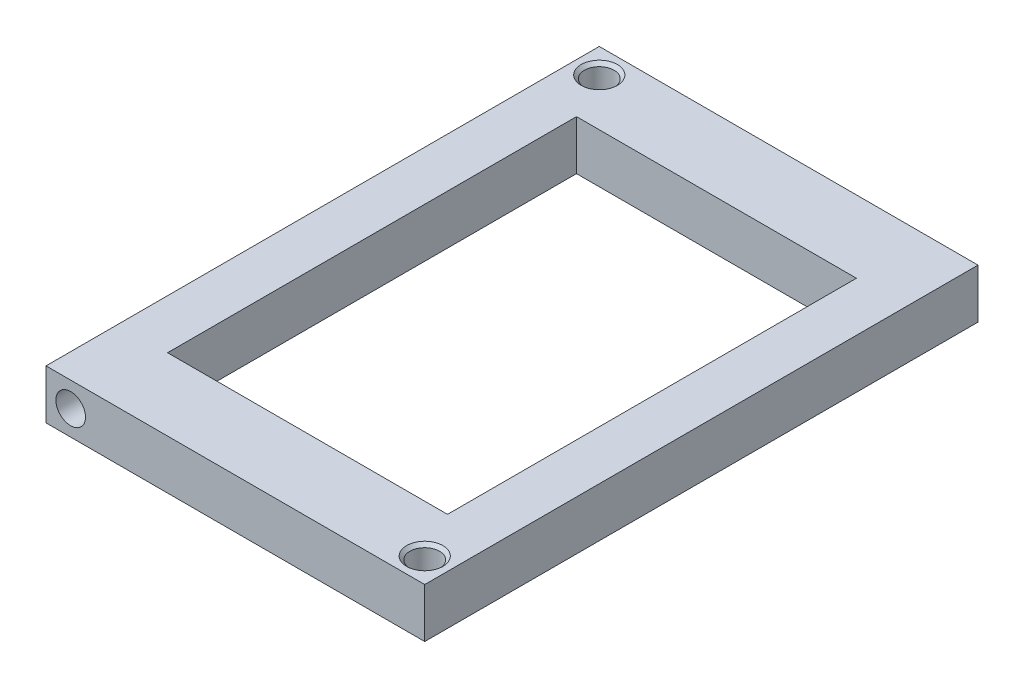
SolidWorks part; units mm, degrees
ref_plane "Plan de face" through (0, 0, 0) normal (0, 0, 1) x (1, 0, 0)
ref_plane "Plan de dessus" through (0, 0, 0) normal (0, 1, 0) x (1, 0, 0)
ref_plane "Plan de droite" through (0, 0, 0) normal (1, 0, 0) x (0, 0, -1)
sketch "Esquisse1" plane through (0, 0, 0) normal (0, 0, 1) x (1, 0, 0)
  line L0 (-15.8423, 13.6674) -> (-23.3423, 13.6674)
  line L1 (-15.8423, 13.6674) -> (26.6577, 13.6674)
  line L5 (-23.3423, 21.1674) -> (34.1577, 21.1674)
  line L6 (-23.3423, 21.1674) -> (-23.3423, 13.6674)
  line L8 (34.1577, 21.1674) -> (34.1577, 13.6674)
  line L9 (26.6577, 13.6674) -> (34.1577, 13.6674)
  line L10 (-23.3423, 21.1674) -> (-15.8423, 13.6674) construction
  dimension "D1" = 42.5
  dimension "D2" = 45
  dimension "D3" = 57.5
  dimension "D5" = 7.5
extrude "Boss.-Extru.1" add sketch "Esquisse1" along normal blind 84
sketch "Esquisse3" plane through (0, 0, 84) normal (0, 0, 1) x (1, 0, 0)
  line L0 (-23.3423, 21.1674) -> (-15.8423, 13.6674) construction
  line L1 (-23.3423, 13.6674) -> (34.1577, 13.6674) construction
  line L2 (-23.3423, 21.1674) -> (-23.3423, 13.6674) construction
  circle A0 centre (-19.5923, 17.4174) radius 2.25
  dimension "D2" = 4.5
  dimension "D1" = 45
extrude "Enlèv. mat.-Extru.1" cut sketch "Esquisse3" against normal blind 25
sketch "Esquisse4" plane through (0, 21.1674, 0) normal (0, 1, 0) x (1, 0, 0)
  line L0 (34.1577, -84) -> (24.6852, -74.5275) construction
  line L1 (26.6577, -84) -> (34.1577, -76.5) construction
  line L2 (34.1577, -84) -> (-23.3423, -84) construction
  line L3 (34.1577, -84) -> (34.1577, 0) construction
  line L4 (-23.3423, 0) -> (34.1577, -84) construction
  line L5 (-23.3423, -84) -> (-23.3423, 0) construction
  line L6 (-15.8423, -10.9565) -> (26.6577, -10.9565)
  line L7 (-15.8423, -10.9565) -> (-15.8423, -73.0435)
  line L8 (-15.8423, -73.0435) -> (26.6577, -73.0435)
  line L9 (26.6577, -10.9565) -> (26.6577, -73.0435)
  circle A0 centre (30.4077, -80.25) radius 2.25
  circle A1 centre (-19.5923, -3.75) radius 2.25
  point P12 (5.4077, -42)
  point P18 (5.4077, -42)
  dimension "D3" = 4.5
  dimension "D1" = 7.5
  dimension "D2" = 45
  dimension "D5" = 42.5
  dimension "D6" = 7.5
  dimension "D4" = 2
extrude "Enlèv. mat.-Extru.2" cut sketch "Esquisse4" against normal up to next
sketch "Esquisse5" plane through (0, 0, 0) normal (0, 0, -1) x (-1, 0, 0)
  line L0 (-34.1577, 21.1674) -> (-26.6577, 13.6674) construction
  line L1 (23.3423, 13.6674) -> (-34.1577, 13.6674) construction
  line L2 (-34.1577, 13.6674) -> (-34.1577, 21.1674) construction
  line L3 (-34.1577, 13.6674) -> (-26.6577, 21.1674) construction
  line L4 (-34.1577, 21.1674) -> (23.3423, 21.1674) construction
  circle A0 centre (-30.4077, 17.4174) radius 2.25
  dimension "D2" = 4.5
  dimension "D1" = 45
extrude "Enlèv. mat.-Extru.3" cut sketch "Esquisse5" against normal blind 25
chamfer "Chanfrein1" distance 0.5 angle 45 2 edges at (30.4077, 21.1674, 82.5) (-19.5923, 21.1674, 6)
